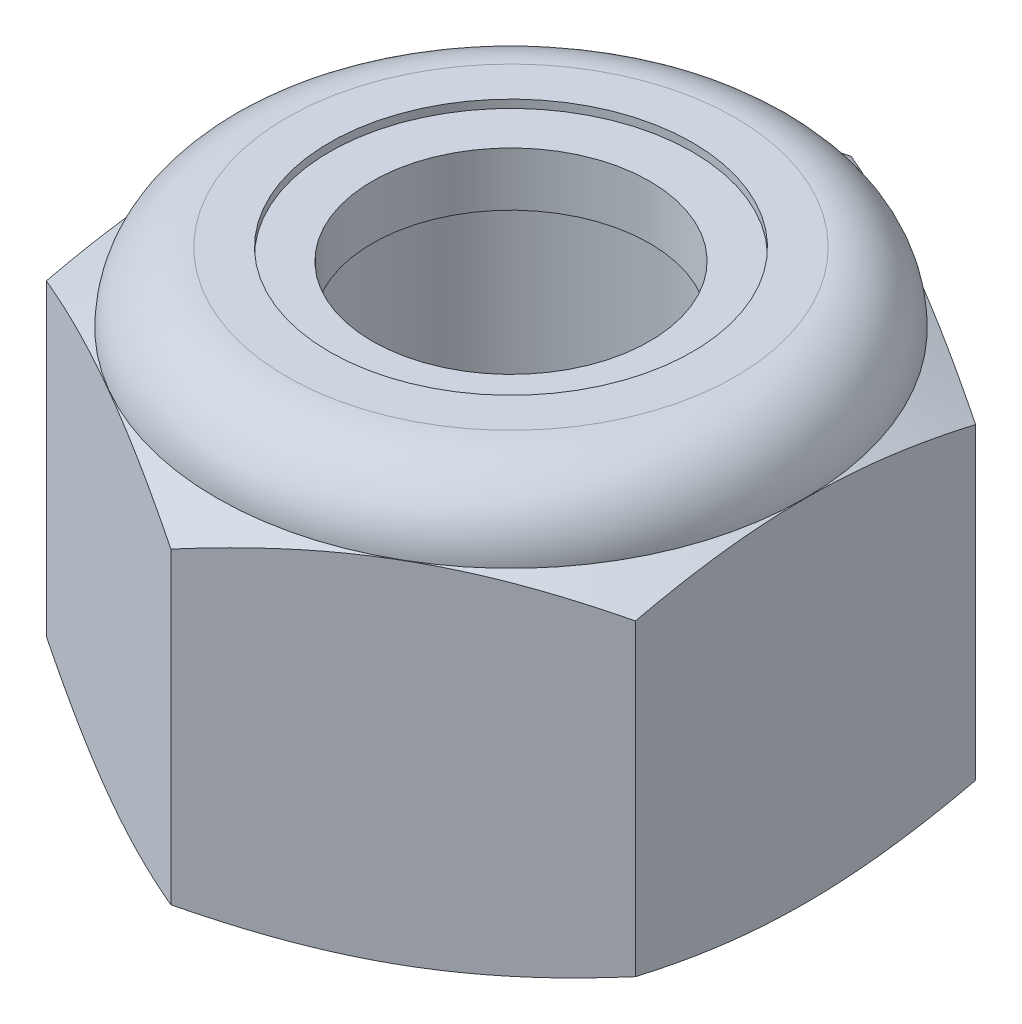
SolidWorks part; units mm, degrees
material "Plain Carbon Steel"
ref_plane "Front Plane" through (0, 0, 0) normal (0, 0, 1) x (1, 0, 0)
ref_plane "Top Plane" through (0, 0, 0) normal (0, 1, 0) x (1, 0, 0)
ref_plane "Right Plane" through (0, 0, 0) normal (1, 0, 0) x (0, 0, -1)
sketch "Sketch1" plane through (0, 0, 0) normal (0, 1, 0) x (1, 0, 0)
  line L0 (0, 0) -> (0, 6.4158) construction
  line L2 (0, 6.4158) -> (-5.5563, 3.2079)
  line L3 (-5.5563, 3.2079) -> (-5.5563, -3.2079)
  line L4 (-5.5563, -3.2079) -> (0, -6.4158)
  line L5 (0, -6.4158) -> (5.5562, -3.2079)
  line L6 (5.5562, -3.2079) -> (5.5562, 3.2079)
  line L7 (5.5562, 3.2079) -> (0, 6.4158)
  circle A0 centre (0, 0) radius 5.5563 construction
  dimension "D1" = 11.1125
extrude "Boss-Extrude1" add sketch "Sketch1" along normal blind 7.9375
sketch "Sketch2" plane through (0, 7.9375, 0) normal (0, 1, 0) x (1, 0, 0)
  circle A0 centre (0, 0) radius 3.175
  dimension "D1" = 6.35
extrude "Cut-Extrude1" cut sketch "Sketch2" against normal through all
sketch "Sketch4" plane through (0, 0, 0) normal (1, 0, 0) x (0, 0, -1)
  line L0 (0, 0) -> (5.5522, 0)
  line L2 (6.4158, 7.9375) -> (6.4158, 0) construction
  line L3 (6.4158, 0.4027) -> (6.4158, 6.214)
  line L4 (6.4158, 6.214) -> (5.5522, 6.6167)
  line L5 (3.2079, 7.9375) -> (6.4158, 7.9375) construction
  line L6 (4.2314, 7.9375) -> (4.2314, 9.2075)
  line L7 (4.2314, 9.2075) -> (7.6858, 9.2075)
  line L8 (7.6858, 9.2075) -> (7.6858, -1.27)
  line L9 (7.6858, -1.27) -> (0, -1.27)
  line L10 (0, -1.27) -> (0, 0)
  line L11 (-3.2079, 0) -> (3.2079, 0) construction
  line L12 (3.2079, 0) -> (6.4158, 0) construction
  line L13 (5.5522, 0) -> (6.4158, 0.4027)
  line L14 (5.5522, 0) -> (5.5522, 6.6167) construction
  line L15 (0, 0) -> (0, 9.6306) construction
  arc A0 (5.5522, 6.6167) -> (4.2314, 7.9375) centre (4.2314, 6.6167) ccw
  dimension "D1" = 1.27
  dimension "D2" = 25
  dimension "D3" = 1.3208
  dimension "D4" = 0.8636
  dimension "D5" = 1.27
revolve "Cut-Revolve1" cut sketch "Sketch4" angle 360 about L15
sketch "Sketch5" plane through (0, 0, 0) normal (1, 0, 0) x (0, 0, -1)
  line L0 (5.3998, 6.6167) -> (0, 6.6167)
  line L1 (5.5522, 6.6167) -> (-5.5522, 6.6167) construction
  line L2 (0, 6.6167) -> (0, 9.1567)
  line L3 (0, 9.1567) -> (3.4216, 9.1567)
  line L4 (3.4216, 9.1567) -> (3.4216, 7.7851)
  line L5 (3.4216, 7.7851) -> (4.2314, 7.7851)
  line L6 (4.2314, 7.7851) -> (4.2314, 7.9375) construction
  line L7 (4.2314, 7.9375) -> (-4.2314, 7.9375) construction
  arc A0 (4.2314, 7.7851) -> (5.3998, 6.6167) centre (4.2314, 6.6167) cw
  arc A1 (5.5522, 6.6167) -> (4.2314, 7.9375) centre (4.2314, 6.6167) ccw construction
  dimension "D1" = 0.1524
  dimension "D2" = 3.4216
  dimension "D3" = 2.54
revolve "Cut-Revolve2" cut sketch "Sketch5" angle 360 about L2
sketch "Sketch6" plane through (0, 0, 0) normal (1, 0, 0) x (0, 0, -1)
  line L1 (2.6162, 6.6929) -> (2.6162, 7.7089)
  line L2 (2.6162, 7.7089) -> (4.2314, 7.7089)
  line L5 (-4.2314, 7.7851) -> (4.2314, 7.7851) construction
  line L6 (5.3209, 6.6929) -> (2.6162, 6.6929)
  line L7 (5.5522, 6.6167) -> (-5.5522, 6.6167) construction
  line L8 (0, 0) -> (0, 7.9375) construction
  line L9 (3.4216, 7.9375) -> (-3.4216, 7.9375) construction
  arc A0 (5.3209, 6.6929) -> (4.2314, 7.7089) centre (4.2314, 6.6167) ccw
  arc A4 (5.3998, 6.6167) -> (4.2314, 7.7851) centre (4.2314, 6.6167) ccw construction
  dimension "D1" = 0.0762
  dimension "D2" = 0.0762
  dimension "D3" = 2.6162
revolve "Revolve1" add sketch "Sketch6" angle 360 about L8
